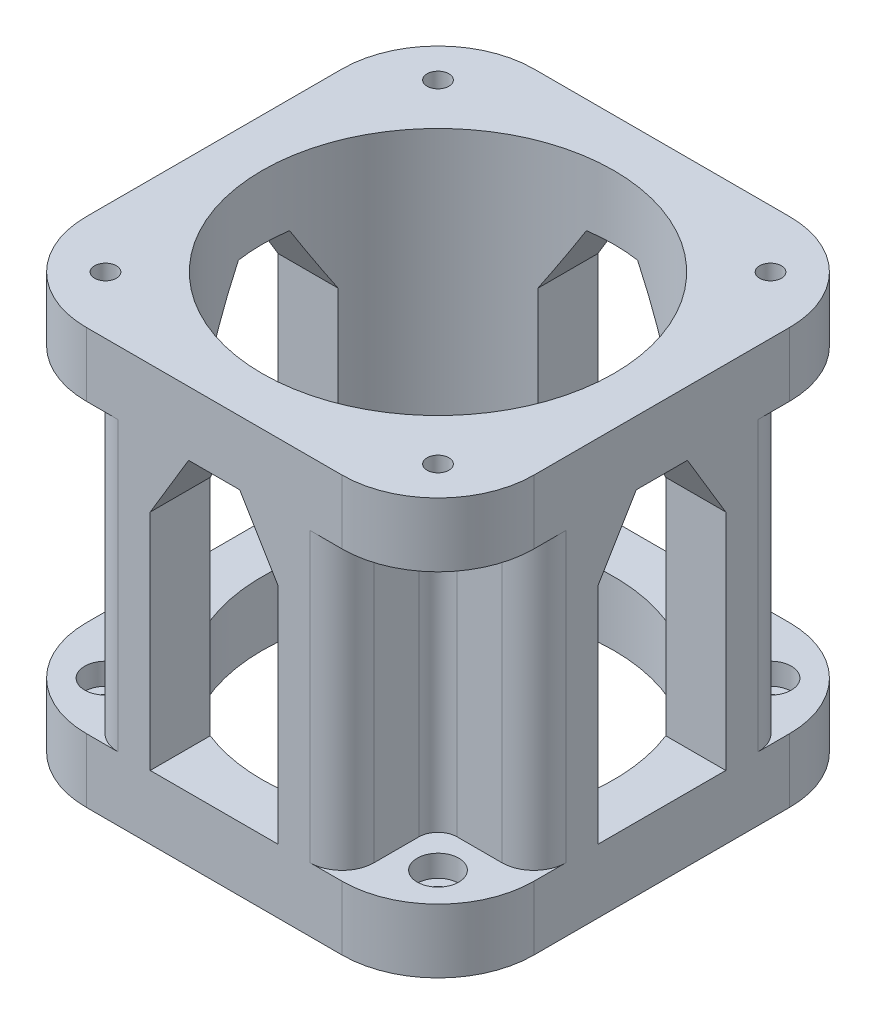
SolidWorks part; units mm, degrees
ref_plane "Front Plane" through (0, 0, 0) normal (0, 0, 1) x (1, 0, 0)
ref_plane "Top Plane" through (0, 0, 0) normal (0, 1, 0) x (1, 0, 0)
ref_plane "Right Plane" through (0, 0, 0) normal (1, 0, 0) x (0, 0, -1)
sketch "Sketch1" plane through (0, 0, 0) normal (0, 1, 0) x (1, 0, 0)
  line L1 (-35, 35) -> (35, 35)
  line L2 (-35, 35) -> (-35, -35)
  line L3 (-35, -35) -> (35, -35)
  line L4 (35, 35) -> (35, -35)
  dimension "D1" = 35
  dimension "D2" = 35
  dimension "D3" = 35
  dimension "D4" = 35
extrude "Boss-Extrude1" add sketch "Sketch1" along normal blind 65
fillet "Fillet1" radius 15 4 edges at (-35, 32.5, -35) (35, 32.5, 35) (-35, 32.5, 35) (35, 32.5, -35)
sketch "Sketch2" plane through (0, 65, 0) normal (0, 1, 0) x (1, 0, 0)
  circle A0 centre (0, 0) radius 27.5
  dimension "D1" = 55
extrude "Cut-Extrude1" cut sketch "Sketch2" against normal blind 65
sketch "Sketch3" plane through (0, 0, -35) normal (0, 0, -1) x (-1, 0, 0)
  line L0 (-10, 10) -> (-10, 45)
  line L1 (-10, 45) -> (-4, 55)
  line L2 (-4, 55) -> (4, 55)
  line L3 (4, 55) -> (10, 45)
  line L4 (10, 45) -> (10, 10)
  line L5 (10, 10) -> (-10, 10)
  line L6 (-20, 65) -> (20, 65) construction
  line L8 (-20, 0) -> (20, 0) construction
  line L9 (20, 0) -> (20, 65) construction
  line L10 (-20, 65) -> (-20, 0) construction
  dimension "D1" = 10
  dimension "D2" = 10
  dimension "D3" = 10
  dimension "D4" = 10
  dimension "D5" = 6
  dimension "D6" = 6
  dimension "D7" = 35
  dimension "D8" = 35
extrude "Cut-Extrude2" cut sketch "Sketch3" against normal through all
sketch "Sketch4" plane through (35, 0, 0) normal (1, 0, 0) x (0, 0, -1)
  line L0 (-10, 10) -> (-10, 45)
  line L1 (-10, 45) -> (-4, 55)
  line L2 (-4, 55) -> (4, 55)
  line L3 (4, 55) -> (10, 45)
  line L4 (10, 45) -> (10, 10)
  line L5 (10, 10) -> (-10, 10)
  line L6 (-20, 0) -> (20, 0) construction
  line L7 (-20, 65) -> (20, 65) construction
  line L8 (-20, 65) -> (-20, 0) construction
  line L9 (20, 0) -> (20, 65) construction
  dimension "D1" = 10
  dimension "D2" = 10
  dimension "D3" = 10
  dimension "D4" = 10
  dimension "D5" = 35
  dimension "D6" = 35
  dimension "D7" = 6
  dimension "D8" = 6
extrude "Cut-Extrude3" cut sketch "Sketch4" against normal through all
sketch "Sketch10" plane through (0, 65, 0) normal (0, 1, 0) x (1, 0, 0)
  line L1 (-20, 35) -> (-35, 35)
  line L2 (-20, 35) -> (-20, 20)
  line L3 (-20, 20) -> (-35, 20)
  line L4 (-35, 35) -> (-35, 20)
  line L5 (-35, -20) -> (-20, -20)
  line L6 (-35, -20) -> (-35, -35)
  line L7 (-35, -35) -> (-20, -35)
  line L8 (-20, -20) -> (-20, -35)
  line L9 (35, -20) -> (20, -20)
  line L10 (35, -20) -> (35, -35)
  line L11 (35, -35) -> (20, -35)
  line L12 (20, -20) -> (20, -35)
  line L13 (35, 20) -> (20, 20)
  line L14 (35, 20) -> (35, 35)
  line L15 (35, 35) -> (20, 35)
  line L16 (20, 20) -> (20, 35)
  arc A0 (-35, -20) -> (-20, -35) centre (-20, -20) ccw construction
  arc A1 (20, -35) -> (35, -20) centre (20, -20) ccw construction
  arc A2 (35, 20) -> (20, 35) centre (20, 20) ccw construction
extrude "Cut-Extrude4" cut sketch "Sketch10" against normal blind 45 from offset 10 offset against normal yes
hole_wizard "CBORE for M3 Hex Socket Head Cap Screw1" positions "Sketch18" profile "Sketch14" counterbore size "M3" standard "ISO"
sketch "Sketch18" plane through (0, 55, 0) normal (0, -1, 0) x (-1, 0, 0)
  line L0 (-20, 20) -> (-35, 20) construction
  line L2 (-20, 35) -> (-20, 20) construction
  line L3 (-20, -20) -> (-20, -35) construction
  line L4 (-35, -20) -> (-20, -20) construction
  line L5 (20, -35) -> (20, -20) construction
  line L6 (20, -20) -> (35, -20) construction
  line L7 (20, 20) -> (20, 35) construction
  line L8 (35, 20) -> (20, 20) construction
  point P0 (26, -26)
  point P2 (-26, -26)
  point P4 (-26, 26)
  point P6 (26, 26)
  dimension "D1" = 6
  dimension "D2" = 6
  dimension "D3" = 6
  dimension "D4" = 6
  dimension "D5" = 6
  dimension "D6" = 6
  dimension "D7" = 6
  dimension "D8" = 6
sketch "Sketch14" plane through (-26, 55, 26) normal (1, 0, 0) x (0, 0, -1)
  line L0 (0, 0) -> (0, 10)
  line L1 (0, 10) -> (1.7, 10)
  line L3 (1.7, 10) -> (1.7, 3.4)
  line L4 (1.7, 3.4) -> (3.25, 3.4)
  line L5 (3.25, 3.4) -> (3.25, 0)
  line L7 (3.25, 0) -> (0, 0)
  line L11 (0, -6.35) -> (0, 107.95) construction
  dimension "Thru Hole Dia." = 3.4
  dimension "Thru Hole Depth" = 10
  dimension "C'Bore Dia." = 6.5
  dimension "C'Bore Depth" = 3.4
fillet "Fillet2" radius 3 4 edges at (20, 32.5, -20) (-20, 32.5, -20) (-20, 32.5, 20) (20, 32.5, 20)
hole_wizard "CBORE for M3 Hex Socket Head Cap Screw2" positions "Sketch19" profile "Sketch20" counterbore size "M3" standard "ISO"
sketch "Sketch19" plane through (0, 10, 0) normal (0, 1, 0) x (1, 0, 0)
  line L0 (-20, -35) -> (-20, -23) construction
  line L1 (-23, -20) -> (-35, -20) construction
  line L2 (-20, 23) -> (-20, 35) construction
  line L3 (-35, 20) -> (-23, 20) construction
  line L4 (20, 35) -> (20, 23) construction
  line L5 (23, 20) -> (35, 20) construction
  line L6 (35, -20) -> (23, -20) construction
  line L8 (20, -23) -> (20, -35) construction
  point P0 (26, -26)
  point P2 (26, 26)
  point P4 (-26, 26)
  point P6 (-26, -26)
  dimension "D1" = 6
  dimension "D2" = 6
  dimension "D3" = 6
  dimension "D4" = 6
  dimension "D5" = 6
  dimension "D6" = 6
  dimension "D7" = 6
  dimension "D8" = 6
sketch "Sketch20" plane through (26, 10, 26) normal (1, 0, 0) x (0, 0, 1)
  line L0 (0, 0) -> (0, 10)
  line L1 (0, 10) -> (1.7, 10)
  line L3 (1.7, 10) -> (1.7, 3.4)
  line L4 (1.7, 3.4) -> (3.25, 3.4)
  line L5 (3.25, 3.4) -> (3.25, 0)
  line L7 (3.25, 0) -> (0, 0)
  line L11 (0, -6.35) -> (0, 107.95) construction
  dimension "Thru Hole Dia." = 3.4
  dimension "Thru Hole Depth" = 10
  dimension "C'Bore Dia." = 6.5
  dimension "C'Bore Depth" = 3.4
fillet "Fillet3" radius 5 8 edges at (20, 32.5, -35) (35, 32.5, -20) (35, 32.5, 20) (20, 32.5, 35) (-20, 32.5, 35) (-35, 32.5, 20) (-35, 32.5, -20) (-20, 32.5, -35)
